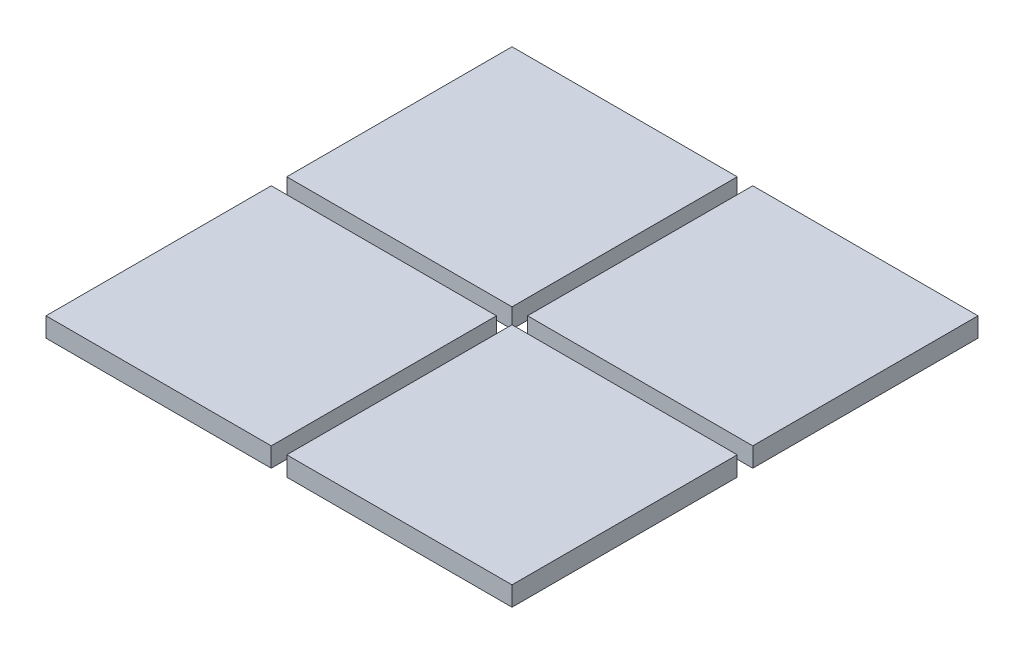
SolidWorks part; units mm, degrees
material "电源线路板"
ref_plane "前视基准面" through (0, 0, 0) normal (0, 0, 1) x (1, 0, 0)
ref_plane "上视基准面" through (0, 0, 0) normal (0, 1, 0) x (1, 0, 0)
ref_plane "右视基准面" through (0, 0, 0) normal (1, 0, 0) x (0, 0, -1)
sketch "草图1" plane through (0, 0, 0) normal (1, 0, 0) x (0, 0, -1)
  line L1 (0, 0) -> (0.2, 0)
  line L2 (0, 0) -> (0, 0.2)
  line L3 (0, 0.2) -> (0.2, 0.2)
  line L4 (0.2, 0) -> (0.2, 0.2)
  line L5 (0, 0) -> (0.2, 0.2) construction
  line L6 (0, 0.2) -> (0.2, 0) construction
  line L7 (0, 0) -> (-0.2, 0)
  line L8 (0, 0) -> (0, -0.2)
  line L9 (0, -0.2) -> (-0.2, -0.2)
  line L10 (-0.2, 0) -> (-0.2, -0.2)
  line L11 (0, 0) -> (-0.2, -0.2) construction
  line L12 (0, -0.2) -> (-0.2, 0) construction
  point P4 (0.1, 0.1)
  point P10 (-0.1, -0.1)
sketch "草图3" plane through (0, 0, 0) normal (1, 0, 0) x (0, 0, -1)
  line L1 (0.2, 0.2) -> (6, 0.2)
  line L2 (0.2, 0.2) -> (0.2, 6)
  line L3 (0.2, 6) -> (6, 6)
  line L4 (6, 0.2) -> (6, 6)
  line L5 (0.2, 0.2) -> (6, 6) construction
  line L6 (0.2, 6) -> (6, 0.2) construction
  line L7 (-0.2, -0.2) -> (-6, -0.2)
  line L8 (-0.2, -0.2) -> (-0.2, -6)
  line L9 (-0.2, -6) -> (-6, -6)
  line L10 (-6, -0.2) -> (-6, -6)
  line L11 (-0.2, -0.2) -> (-6, -6) construction
  line L12 (-0.2, -6) -> (-6, -0.2) construction
  line L13 (0.2, -0.2) -> (6, -0.2)
  line L14 (0.2, -0.2) -> (0.2, -6)
  line L15 (0.2, -6) -> (6, -6)
  line L16 (6, -0.2) -> (6, -6)
  line L17 (0.2, -0.2) -> (6, -6) construction
  line L18 (0.2, -6) -> (6, -0.2) construction
  line L19 (-0.2, 0.2) -> (-6, 0.2)
  line L20 (-0.2, 0.2) -> (-0.2, 6)
  line L21 (-0.2, 6) -> (-6, 6)
  line L22 (-6, 0.2) -> (-6, 6)
  line L23 (-0.2, 0.2) -> (-6, 6) construction
  line L24 (-0.2, 6) -> (-6, 0.2) construction
  point P4 (3.1, 3.1)
  point P10 (-3.1, -3.1)
  point P16 (3.1, -3.1)
  point P21 (-3.1, 3.1)
extrude "凸台-拉伸1" add sketch "草图3" along normal blind 0.5
sketch "草图4" plane through (0, 0, 0) normal (1, 0, 0) x (0, 0, -1)
  line L1 (0.5, -0.5) -> (-0.5, -0.5)
  line L2 (0.5, -0.5) -> (0.5, 0.5)
  line L3 (0.5, 0.5) -> (-0.5, 0.5)
  line L4 (-0.5, -0.5) -> (-0.5, 0.5)
  line L5 (0.5, -0.5) -> (-0.5, 0.5) construction
  line L6 (0.5, 0.5) -> (-0.5, -0.5) construction
  circle A0 centre (-0.5, -0.5) radius 0.1
  point P4 (0, 0)
sketch3d "3D草图1"
  line L8 (0, -0.5, 0.5) -> (2.8, -0.5, 0.5)
  line L17 (3, -0.2414, 0.2414) -> (3, -0.3586, 0.3586)
  line L18 (3.2, -0.1, 0.1) -> (6, -0.1, 0.1)
  arc A0 (2.8, -0.5, 0.5) -> (3, -0.3586, 0.3586) centre (2.8, -0.3586, 0.3586) ccw
  arc A1 (3.2, -0.1, 0.1) -> (3, -0.2414, 0.2414) centre (3.2, -0.2414, 0.2414) ccw
  point P11 (3, -0.5, 0.5)
  point P12 (2.8, -0.2172, 0.5)
  point P15 (3, -0.1, 0.1)
  point P16 (3.2, -0.1, 0.3828)
  dimension "D1" = 0.2
  dimension "D2" = 0.2
sketch "草图31" plane through (0, 0, 0) normal (0, 0, 1) x (1, 0, 0)
  line L0 (10, 0.5) -> (10, 5.5)
  line L1 (9.5, 0) -> (6.0015, 0)
  arc A0 (9.5, 0) -> (10, 0.5) centre (9.5, 0.5) ccw
  dimension "D1" = 0.5
move or copy body "实体-移动/复制2" bodies to move or copy 107 109 106 108 copy no rotation origin (0, 0, 0) rotation axis (0, 0, 1) rotation angle 90
sketch "草图32" plane through (0, 0, 0) normal (0, 1, 0) x (1, 0, 0)
  line L0 (0, 0) -> (-0.2, 0.2)
  line L3 (0, 0) -> (0.2, -0.2)
